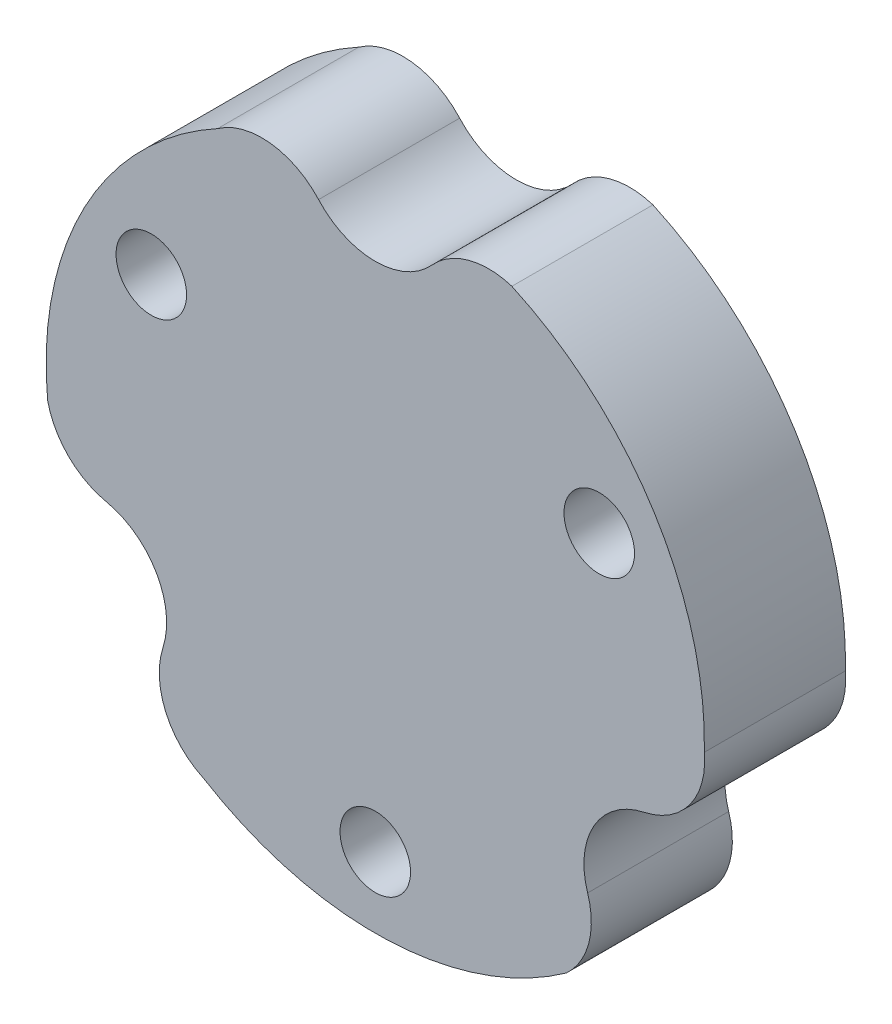
SolidWorks part; units mm, degrees
ref_plane "Plan de face" through (0, 0, 0) normal (0, 0, 1) x (1, 0, 0)
ref_plane "Plan de dessus" through (0, 0, 0) normal (0, 1, 0) x (1, 0, 0)
ref_plane "Plan de droite" through (0, 0, 0) normal (1, 0, 0) x (0, 0, -1)
sketch "Esquisse1" plane through (0, 0, 0) normal (0, 0, 1) x (1, 0, 0)
  line L0 (9.5263, 5.5) -> (0, -11) construction
  line L1 (0, -11) -> (-9.5263, 5.5) construction
  line L2 (-9.5263, 5.5) -> (9.5263, 5.5) construction
  arc A12 (-2.411, 11.8207) -> (2.411, 11.8207) centre (0, 14) ccw
  arc A16 (5.8094, 12.7378) -> (2.411, 11.8207) centre (4.8221, 9.6414) ccw
  arc A17 (-2.411, 11.8207) -> (-6.7074, 12.2887) centre (-4.8221, 9.6414) ccw
  arc A18 (-6.7074, 12.2887) -> (-13.9359, -1.3378) centre (0, 0) ccw
  arc A19 (8.1265, -11.4) -> (9.0315, -7.9984) centre (5.9386, -8.9967) ccw
  arc A20 (11.4425, -3.8223) -> (9.0315, -7.9984) centre (12.1244, -7) ccw
  arc A21 (11.4425, -3.8223) -> (13.996, -0.3356) centre (10.7607, -0.6447) ccw
  arc A23 (-13.9359, -1.3378) -> (-11.4425, -3.8223) centre (-10.7607, -0.6447) ccw
  arc A24 (-9.0315, -7.9984) -> (-11.4425, -3.8223) centre (-12.1244, -7) ccw
  arc A25 (-9.0315, -7.9984) -> (-7.2886, -11.9531) centre (-5.9386, -8.9967) ccw
  arc A27 (-7.2886, -11.9531) -> (8.1265, -11.4) centre (0, 0) ccw
  arc A28 (13.996, -0.3356) -> (5.8094, 12.7378) centre (0, 0) ccw
  circle A30 centre (0, 0) radius 11 construction
  circle A31 centre (9.5263, 5.5) radius 1.5
  circle A32 centre (0, -11) radius 1.5
  circle A33 centre (-9.5263, 5.5) radius 1.5
  point P6 (9.5263, 5.5)
  point P31 (0, 0)
  dimension "D2" = 3
  dimension "D3" = 11
  dimension "D4" = 11
  dimension "D5" = 11
  dimension "D8" = 14
  dimension "D9" = 3.25
  dimension "D11" = 3.25
  dimension "D6" = 60
  dimension "D7" = 60
  dimension "D14" = 10.78
  dimension "D15" = 10.78
extrude "Boss.-Extru.2" add sketch "Esquisse1" along normal blind 6
